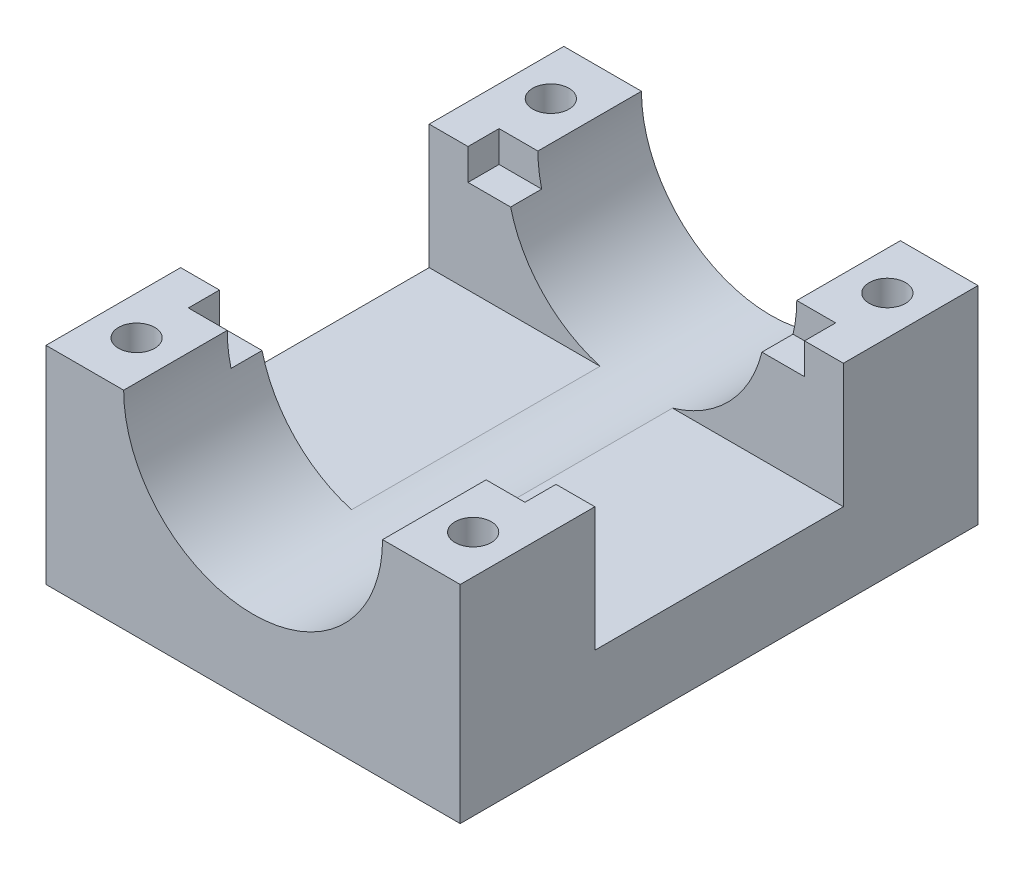
SolidWorks part; units mm, degrees
ref_plane "Alzado" through (0, 0, 0) normal (0, 0, 1) x (1, 0, 0)
ref_plane "Planta" through (0, 0, 0) normal (0, 1, 0) x (1, 0, 0)
ref_plane "Vista lateral" through (0, 0, 0) normal (1, 0, 0) x (0, 0, -1)
sketch "Croquis1" plane through (0, 0, 0) normal (0, 1, 0) x (1, 0, 0)
  line L1 (0, 0) -> (40, 0)
  line L2 (0, 0) -> (0, 50)
  line L3 (0, 50) -> (40, 50)
  line L4 (40, 0) -> (40, 50)
  dimension "D1" = 50
  dimension "D2" = 40
extrude "Saliente-Extruir1" add sketch "Croquis1" along normal blind 20
sketch "Croquis2" plane through (0, 0, 0) normal (0, 0, 1) x (1, 0, 0)
  line L0 (0, 20) -> (40, 20) construction
  circle A0 centre (20, 20) radius 12.5
  dimension "D1" = 25
extrude "Cortar-Extruir1" cut sketch "Croquis2" against normal through all
sketch "Croquis3" plane through (0, 20, 0) normal (0, 1, 0) x (1, 0, 0)
  line L1 (7.5, 50) -> (0, 50) construction
  line L6 (0, 50) -> (0, 0) construction
  circle A0 centre (3.75, 45) radius 1.75
  circle A1 centre (36.25, 45) radius 1.75
  circle A2 centre (36.25, 5) radius 1.75
  circle A3 centre (3.75, 5) radius 1.75
  dimension "D1" = 5
  dimension "D5" = 3.5
  dimension "D2" = 3.75
  dimension "D3" = 2
  dimension "D4" = 2
extrude "Cortar-Extruir2" cut sketch "Croquis3" against normal through all
sketch "Croquis4" plane through (40, 0, 0) normal (1, 0, 0) x (0, 0, -1)
  line L2 (0, 20) -> (50, 20) construction
  line L3 (25, 20) -> (37, 20)
  line L4 (37, 20) -> (37, 8)
  line L5 (37, 8) -> (13, 8)
  line L6 (13, 8) -> (13, 20)
  line L7 (13, 20) -> (25, 20)
  dimension "D1" = 12
  dimension "D2" = 12
  dimension "D3" = 24
  dimension "D4" = 12
extrude "Cortar-Extruir3" cut sketch "Croquis4" against normal through all
sketch "Croquis5" plane through (0, 20, 0) normal (0, 1, 0) x (1, 0, 0)
  line L17 (3.75, 37) -> (3.75, 40)
  line L18 (0, 37) -> (7.5, 37) construction
  line L19 (3.75, 40) -> (8.75, 40)
  line L20 (8.75, 40) -> (8.75, 37)
  line L21 (0, 37) -> (16.5, 37) construction
  line L22 (8.75, 37) -> (3.75, 37)
  line L23 (36.25, 37) -> (36.25, 40)
  line L24 (32.5, 37) -> (40, 37) construction
  line L25 (36.25, 40) -> (31.25, 40)
  line L26 (31.25, 40) -> (31.25, 37)
  line L27 (23.5, 37) -> (32.5, 37) construction
  line L28 (31.25, 37) -> (36.25, 37)
  line L29 (36.25, 13) -> (36.25, 10)
  line L30 (32.5, 13) -> (40, 13) construction
  line L31 (36.25, 10) -> (31.25, 10)
  line L32 (31.25, 10) -> (31.25, 13)
  line L33 (23.5, 13) -> (40, 13) construction
  line L34 (31.25, 13) -> (36.25, 13)
  line L35 (3.75, 10) -> (3.75, 13)
  line L36 (0, 13) -> (7.5, 13) construction
  line L37 (3.75, 13) -> (8.75, 13)
  line L38 (0, 13) -> (16.5, 13) construction
  line L39 (8.75, 13) -> (8.75, 10)
  line L40 (8.75, 10) -> (3.75, 10)
  dimension "D1" = 3
  dimension "D2" = 5
  dimension "D3" = 5
  dimension "D4" = 3
extrude "Cortar-Extruir4" cut sketch "Croquis5" against normal blind 3
